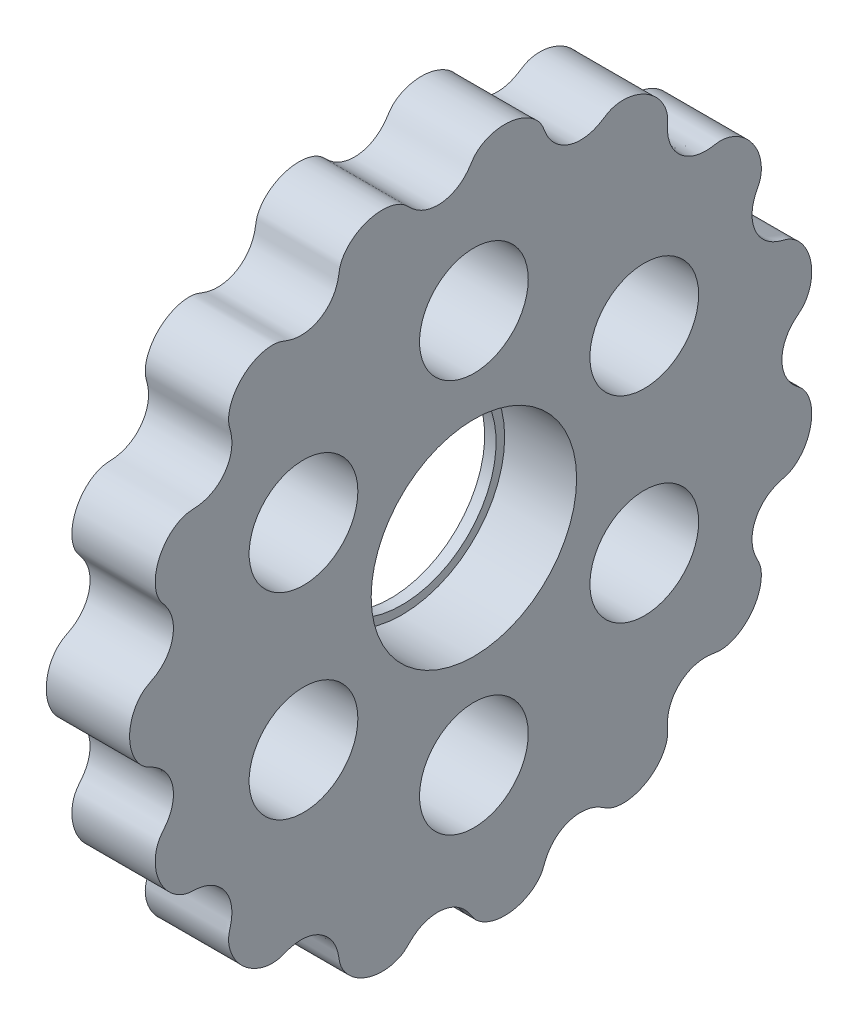
SolidWorks part; units mm, degrees
ref_plane "Front Plane" through (0, 0, 0) normal (0, 0, 1) x (1, 0, 0)
ref_plane "Top Plane" through (0, 0, 0) normal (0, 1, 0) x (1, 0, 0)
ref_plane "Right Plane" through (0, 0, 0) normal (1, 0, 0) x (0, 0, -1)
sketch "Sketch2" plane through (0, 0, 0) normal (0, 0, 1) x (1, 0, 0)
  line L0 (0, 0) -> (58.591, 0) construction
  line L2 (0, 0) -> (18.4, 0)
  line L3 (0, 0) -> (0, 2.5)
  line L4 (0, 2.5) -> (18.4, 2.5)
  line L5 (18.4, 0) -> (18.4, 2.5)
  line L6 (6.0094, 2.5) -> (6.0094, 6)
  line L11 (6.0094, 6) -> (9.9794, 6)
  line L16 (12.9794, 6) -> (12.9794, 3)
  line L17 (12.9794, 3) -> (13.6398, 3)
  line L18 (13.6398, 3) -> (13.6398, 2.5)
  line L19 (13.6398, 2.5) -> (6.0094, 2.5)
  line L22 (13.6398, 2.5) -> (16.1198, 2.5)
  line L23 (13.6398, 2.5) -> (13.6398, 4)
  line L24 (13.6398, 4) -> (16.1198, 4)
  line L25 (16.1198, 2.5) -> (16.1198, 4)
  line L27 (6.0094, 6) -> (9.9794, 6)
  line L28 (6.0094, 6) -> (6.0094, 9)
  line L29 (6.0094, 9) -> (9.9794, 9)
  line L30 (9.9794, 6) -> (9.9794, 9)
  line L31 (6.0094, 9) -> (6.0094, 8.25)
  line L32 (6.0094, 8.25) -> (5.0094, 8.25)
  line L33 (8.6609, 22.001) -> (8.6609, 12.476) construction
  line L34 (5.0094, 12.476) -> (12.3124, 12.476)
  line L35 (9.9794, 9) -> (12.3124, 9)
  line L36 (5.0094, 7.9375) -> (1.7709, 7.9375)
  line L37 (5.0094, 8.25) -> (5.0094, 12.476)
  line L38 (5.0094, 7.9375) -> (5.0094, 13.9365)
  line L39 (5.0094, 13.9365) -> (1.7709, 13.9365)
  line L40 (1.7709, 7.9375) -> (1.7709, 13.9365)
  line L41 (5.0094, 22.001) -> (12.3124, 22.001)
  line L42 (5.0094, 22.001) -> (5.0094, 30.1625)
  line L43 (5.0094, 30.1625) -> (12.3124, 30.1625)
  line L44 (12.3124, 22.001) -> (12.3124, 30.1625)
  line L49 (16.6398, 22.001) -> (16.6398, 7.5)
  line L51 (23.0198, 7.5) -> (23.0198, 6.5)
  line L54 (16.1198, 4) -> (13.6398, 4)
  line L56 (18.0398, 7.5) -> (23.0198, 7.5)
  line L57 (13.3124, 22.001) -> (16.6398, 22.001)
  line L58 (16.1198, 3.5) -> (20.0198, 3.5)
  line L59 (29.9098, 14) -> (26.9098, 11)
  line L60 (4.0094, 31.75) -> (18.0398, 31.75)
  line L61 (18.0398, 7.5) -> (23.0198, 7.5)
  line L62 (18.0398, 7.5) -> (18.0398, 12)
  line L63 (18.0398, 12) -> (23.0198, 12)
  line L64 (23.0198, 7.5) -> (23.0198, 12)
  line L65 (18.0398, 31.75) -> (18.0398, 12)
  line L66 (23.0198, 11) -> (26.9098, 11)
  line L67 (34.8098, 23) -> (31.3098, 19.5)
  line L68 (35.8098, 31) -> (38.7998, 33.99)
  line L69 (29.9098, 14) -> (29.9098, 15)
  line L70 (29.9098, 15) -> (22.9398, 15)
  line L71 (22.9398, 15) -> (21.0398, 15)
  line L72 (18.0398, 7.5) -> (16.6398, 7.5)
  line L73 (21.0398, 15) -> (21.0398, 43)
  line L74 (19.6115, 40) -> (9.6516, 40)
  line L75 (9.6516, 40) -> (4.0094, 40)
  line L76 (21.0398, 43) -> (19.6115, 43)
  line L77 (22.9398, 15) -> (29.9098, 15)
  line L78 (22.9398, 15) -> (22.9398, 21)
  line L79 (22.9398, 21) -> (29.9098, 21)
  line L80 (29.9098, 15) -> (29.9098, 21)
  line L81 (9.6516, 40) -> (19.6115, 40)
  line L82 (9.6516, 40) -> (9.6516, 50)
  line L83 (9.6516, 50) -> (19.6115, 50)
  line L84 (19.6115, 40) -> (19.6115, 50)
  line L85 (4.0094, 40) -> (4.0094, 31.75)
  line L86 (12.9794, 3) -> (12.9794, 2.5)
  line L87 (31.3098, 19.5) -> (29.9098, 19.5)
  line L88 (21.4694, 63.5) -> (21.4694, 51.308)
  line L89 (21.4694, 63.5) -> (25.9398, 63.5)
  line L90 (25.9398, 63.5) -> (25.9398, 25)
  line L91 (27.8398, 25) -> (25.9398, 25)
  line L92 (9.6516, 48) -> (8.2233, 48)
  line L93 (8.2233, 48) -> (8.2233, 53.476)
  line L94 (8.2233, 53.476) -> (19.6115, 53.476)
  line L95 (19.6115, 53.476) -> (19.6115, 50)
  line L96 (13.9174, 63.001) -> (13.9174, 53.476) construction
  line L97 (8.2233, 63.001) -> (19.6115, 63.001)
  line L98 (8.2233, 63.001) -> (8.2233, 68.2625)
  line L99 (8.2233, 68.2625) -> (19.6115, 68.2625)
  line L100 (19.6115, 63.001) -> (19.6115, 68.2625)
  line L101 (12.9794, 6) -> (11.9794, 6)
  line L102 (8.2233, 44.825) -> (4.9848, 44.825)
  line L103 (8.2233, 44.825) -> (8.2233, 54.9365)
  line L104 (8.2233, 54.9365) -> (4.9848, 54.9365)
  line L106 (9.9794, 6) -> (10.8794, 6)
  line L107 (27.8398, 25) -> (34.8098, 25)
  line L108 (34.8098, 25) -> (34.8098, 23)
  line L109 (0, 0) -> (-2, 0)
  line L110 (0, 0) -> (0, 11)
  line L111 (27.8398, 25) -> (34.8098, 25)
  line L112 (27.8398, 25) -> (27.8398, 32.5)
  line L113 (27.8398, 32.5) -> (34.8098, 32.5)
  line L114 (34.8098, 25) -> (34.8098, 32.5)
  line L115 (35.8098, 31) -> (34.8098, 31)
  line L116 (27.8398, 32.5) -> (27.8398, 64.5)
  line L117 (20.5849, 74.025) -> (6.2499, 74.025)
  line L118 (6.2499, 74.025) -> (6.2499, 76.2)
  line L119 (38.7998, 47.29) -> (30.8398, 55.25)
  line L120 (0, 11) -> (-2, 11)
  line L121 (38.7998, 43.815) -> (30.8623, 43.815)
  line L123 (-4.8152, 69.85) -> (1.5348, 76.2)
  line L124 (38.7998, 47.29) -> (38.7998, 33.99)
  line L125 (-2, 0) -> (-2, 11)
  line L126 (38.7998, 37.465) -> (30.8623, 37.465)
  line L127 (30.8623, 43.815) -> (30.8623, 37.465)
  line L128 (6.0094, 2.5) -> (6.0094, 0)
  line L129 (-0.0152, 63.5) -> (-0.0152, 30)
  line L132 (4.9848, 63.5) -> (-0.0152, 63.5)
  line L136 (-1.8152, 30) -> (-11.7752, 30)
  line L138 (-13.7752, 25.4) -> (-2, 25.4)
  line L139 (-2, 25.4) -> (-2, 11.5)
  line L140 (27.8398, 64.5) -> (20.5849, 64.5)
  line L141 (-1.8152, 30) -> (-11.7752, 30)
  line L142 (-1.8152, 30) -> (-1.8152, 39)
  line L143 (-1.8152, 39) -> (-11.7752, 39)
  line L144 (-11.7752, 30) -> (-11.7752, 39)
  line L145 (20.5849, 64.5) -> (20.5849, 74.025)
  line L146 (-12.7752, 37) -> (-12.7752, 47.29)
  line L147 (-12.7752, 37) -> (-11.7752, 37)
  line L148 (30.8398, 55.25) -> (30.8398, 76.2)
  line L149 (11.9794, 6) -> (11.9794, 5.45)
  line L154 (-2, 11.5) -> (0.5, 11.5)
  line L155 (4.9848, 60.6197) -> (24.0348, 60.6197)
  line L160 (4.9848, 60.6197) -> (4.9848, 55.8572)
  line L161 (4.9848, 55.8572) -> (24.0348, 55.8572)
  line L166 (24.0348, 60.6197) -> (24.0348, 55.8572)
  line L167 (4.9848, 60.6197) -> (24.0348, 55.8572) construction
  line L172 (4.9848, 55.8572) -> (24.0348, 60.6197) construction
  line L173 (24.0348, 62.2072) -> (25.9398, 62.2072)
  line L174 (11.9794, 5.45) -> (10.8794, 5.45)
  line L175 (10.8794, 6) -> (10.8794, 5.45)
  line L176 (24.0348, 62.2072) -> (24.0348, 54.2697)
  line L177 (24.0348, 54.2697) -> (25.9398, 54.2697)
  line L178 (25.9398, 62.2072) -> (25.9398, 54.2697)
  line L179 (24.0348, 62.2072) -> (25.9398, 54.2697) construction
  line L180 (24.0348, 54.2697) -> (25.9398, 62.2072) construction
  line L181 (3, 19.6197) -> (15.7, 19.6197)
  line L182 (3, 19.6197) -> (3, 14.8572)
  line L183 (3, 14.8572) -> (15.7, 14.8572)
  line L184 (15.7, 19.6197) -> (15.7, 14.8572)
  line L185 (3, 19.6197) -> (15.7, 14.8572) construction
  line L186 (3, 14.8572) -> (15.7, 19.6197) construction
  line L187 (15.7, 21.2072) -> (16.6398, 21.2072)
  line L188 (15.7, 21.2072) -> (15.7, 13.2697)
  line L189 (15.7, 13.2697) -> (16.6398, 13.2697)
  line L190 (16.6398, 21.2072) -> (16.6398, 13.2697)
  line L191 (15.7, 21.2072) -> (16.6398, 13.2697) construction
  line L192 (15.7, 13.2697) -> (16.6398, 21.2072) construction
  line L193 (0.5, 11.5) -> (0.5, 6.9375)
  line L194 (0.5, 6.9375) -> (1.7709, 6.9375)
  line L195 (23.0198, 6.5) -> (20.0198, 3.5)
  line L196 (4.9848, 63.5) -> (4.9848, 54.9365)
  line L197 (3, 43.825) -> (4.9848, 43.825)
  line L198 (1.7709, 6.9375) -> (1.7709, 7.9375)
  line L199 (6.0094, 0) -> (12.9794, 0)
  line L200 (12.9794, 0) -> (12.9794, 2.5)
  line L201 (18.0398, 31.75) -> (18.0398, 35.875)
  line L202 (18.0398, 35.875) -> (21.0398, 35.875)
  line L203 (30.8398, 76.2) -> (6.2499, 76.2)
  line L204 (2.8049, 69.85) -> (7.2499, 69.85) construction
  line L205 (7.2499, 67.4688) -> (26.2999, 67.4688)
  line L206 (7.2499, 74.025) -> (7.2499, 64.5)
  line L207 (7.2499, 64.5) -> (-1.8152, 64.5)
  line L208 (-1.8152, 64.5) -> (-1.8152, 39)
  line L209 (-12.7752, 47.29) -> (-4.8152, 55.25)
  line L210 (-4.8152, 55.25) -> (-4.8152, 69.85)
  line L211 (7.2499, 67.4688) -> (7.2499, 72.2312)
  line L212 (7.2499, 72.2312) -> (26.2999, 72.2313)
  line L213 (26.2999, 67.4688) -> (26.2999, 72.2313)
  line L214 (26.2999, 73.8187) -> (30.8398, 73.8187)
  line L215 (26.2999, 73.8187) -> (26.2999, 65.8813)
  line L216 (26.2999, 65.8813) -> (30.8398, 65.8813)
  line L217 (30.8398, 73.8187) -> (30.8398, 65.8813)
  line L218 (2.8049, 72.2313) -> (25.0299, 72.2313)
  line L219 (2.8049, 72.2313) -> (2.8049, 67.4687)
  line L220 (2.8049, 67.4687) -> (25.0299, 67.4687)
  line L221 (25.0299, 72.2313) -> (25.0299, 67.4687)
  line L222 (25.0299, 69.85) -> (20.5849, 69.85) construction
  line L223 (21.4694, 51.308) -> (22.9398, 51.308)
  line L224 (22.9398, 51.308) -> (22.9398, 21)
  line L225 (13.6398, 4) -> (13.6398, 12.2697)
  line L226 (13.6398, 12.2697) -> (13.3124, 12.2697)
  line L227 (13.3124, 12.2697) -> (13.3124, 22.001)
  line L228 (12.3124, 9) -> (12.3124, 12.476)
  line L229 (-1.8152, 30) -> (-0.0152, 30)
  line L230 (8.2233, 65.6317) -> (2.8049, 65.6317) construction
  line L231 (19.6115, 65.6317) -> (25.0299, 65.6317) construction
  line L232 (1.5348, 76.2) -> (6.2499, 76.2)
  line L233 (-11.7752, 30) -> (-13.7752, 30)
  line L234 (-13.7752, 30) -> (-13.7752, 25.4)
  line L235 (3, 13.9365) -> (3, 43.825)
  line L236 (4.9848, 54.9365) -> (4.9848, 44.825)
  line L237 (4.9848, 43.825) -> (4.9848, 44.825)
  circle A0 centre (26.8898, 25.95) radius 0.95
  circle A1 centre (21.9898, 15.95) radius 0.95
  circle A2 centre (17.3398, 8.2) radius 0.7
  circle A3 centre (10.4294, 6.45) radius 0.45
  circle A4 centre (-0.9152, 30.9) radius 0.9
  point P7 (24.9873, 58.2385)
  point P131 (16.1699, 17.2385)
  point P135 (14.5098, 58.2385)
  point P146 (9.35, 17.2385)
sketch "Sketch3" plane through (0, 0, 0) normal (1, 0, 0) x (0, 0, -1)
  line L0 (0, 0) -> (0, 69.85) construction
  line L1 (0, 0) -> (13.6271, 68.5079) construction
  line L2 (0, 0) -> (0, 58.2385) construction
  line L3 (0, 0) -> (50.436, 29.1192) construction
  line L4 (0, 0) -> (0, 31.75) construction
  line L5 (0, 0) -> (12.1502, 29.3332) construction
  line L6 (0, 0) -> (0, 17.2385) construction
  line L7 (0, 0) -> (14.929, 8.6192) construction
  line L8 (0, 0) -> (0, 58.2385) construction
  line L9 (0, 0) -> (50.436, 29.1192) construction
  line L10 (0, 0) -> (5.9583, 29.9542) construction
  line L11 (0, 0) -> (16.9677, 25.394) construction
  circle A0 centre (0, 0) radius 69.85 construction
  circle A1 centre (0, 0) radius 58.2385 construction
  circle A2 centre (0, 0) radius 31.75 construction
  circle A3 centre (0, 0) radius 17.2385 construction
  circle A4 centre (0, 69.85) radius 3.175
  circle A5 centre (0, 58.2385) radius 4.7625
  circle A6 centre (0, 31.75) radius 3.175
  circle A7 centre (0, 17.2385) radius 4.7625
  circle A8 centre (13.6271, 68.5079) radius 3.175
  circle A9 centre (26.7304, 64.533) radius 3.175
  circle A10 centre (38.8066, 58.0782) radius 3.175
  circle A11 centre (49.3914, 49.3914) radius 3.175
  circle A12 centre (58.0782, 38.8066) radius 3.175
  circle A13 centre (64.533, 26.7304) radius 3.175
  circle A14 centre (68.5079, 13.6271) radius 3.175
  circle A15 centre (69.85, 0) radius 3.175
  circle A16 centre (68.5079, -13.6271) radius 3.175
  circle A17 centre (64.533, -26.7304) radius 3.175
  circle A18 centre (58.0782, -38.8066) radius 3.175
  circle A19 centre (49.3914, -49.3914) radius 3.175
  circle A20 centre (38.8066, -58.0782) radius 3.175
  circle A21 centre (26.7304, -64.533) radius 3.175
  circle A22 centre (13.6271, -68.5079) radius 3.175
  circle A23 centre (0, -69.85) radius 3.175
  circle A24 centre (-13.6271, -68.5079) radius 3.175
  circle A25 centre (-26.7304, -64.533) radius 3.175
  circle A26 centre (-38.8066, -58.0782) radius 3.175
  circle A27 centre (-49.3914, -49.3914) radius 3.175
  circle A28 centre (-58.0782, -38.8066) radius 3.175
  circle A29 centre (-64.533, -26.7304) radius 3.175
  circle A30 centre (-68.5079, -13.6271) radius 3.175
  circle A31 centre (-69.85, 0) radius 3.175
  circle A32 centre (-68.5079, 13.6271) radius 3.175
  circle A33 centre (-64.533, 26.7304) radius 3.175
  circle A34 centre (-58.0782, 38.8066) radius 3.175
  circle A35 centre (-49.3914, 49.3914) radius 3.175
  circle A36 centre (-38.8066, 58.0782) radius 3.175
  circle A37 centre (-26.7304, 64.533) radius 3.175
  circle A38 centre (-13.6271, 68.5079) radius 3.175
  circle A47 centre (50.436, 29.1192) radius 4.7625
  circle A48 centre (50.436, -29.1192) radius 4.7625
  circle A49 centre (0, -58.2385) radius 4.7625
  circle A50 centre (-50.436, -29.1192) radius 4.7625
  circle A51 centre (-50.436, 29.1192) radius 4.7625
  circle A58 centre (12.1502, 29.3332) radius 3.175
  circle A59 centre (22.4506, 22.4506) radius 3.175
  circle A60 centre (29.3332, 12.1502) radius 3.175
  circle A61 centre (31.75, 0) radius 3.175
  circle A62 centre (29.3332, -12.1502) radius 3.175
  circle A63 centre (22.4506, -22.4506) radius 3.175
  circle A64 centre (12.1502, -29.3332) radius 3.175
  circle A65 centre (0, -31.75) radius 3.175
  circle A66 centre (-12.1502, -29.3332) radius 3.175
  circle A67 centre (-22.4506, -22.4506) radius 3.175
  circle A68 centre (-29.3332, -12.1502) radius 3.175
  circle A69 centre (-31.75, 0) radius 3.175
  circle A70 centre (-29.3332, 12.1502) radius 3.175
  circle A71 centre (-22.4506, 22.4506) radius 3.175
  circle A72 centre (14.929, 8.6192) radius 4.7625
  circle A73 centre (14.929, -8.6192) radius 4.7625
  circle A74 centre (0, -17.2385) radius 4.7625
  circle A75 centre (-14.929, -8.6192) radius 4.7625
  circle A76 centre (-14.929, 8.6192) radius 4.7625
  circle A77 centre (0, 0) radius 50
  circle A78 centre (0, 0) radius 9
  circle A79 centre (-12.1502, 29.3332) radius 3.175
  circle A80 centre (0, 0) radius 76.2
  circle A81 centre (0, 0) radius 74.025
  circle A82 centre (0, 69.85) radius 3.9687
  circle A83 centre (49.3914, 49.3914) radius 3.9687
  circle A84 centre (69.85, 0) radius 3.9688
  circle A85 centre (49.3914, -49.3914) radius 3.9687
  circle A86 centre (0, -69.85) radius 3.9687
  circle A87 centre (-49.3914, -49.3914) radius 3.9687
  circle A88 centre (-69.85, 0) radius 3.9688
  circle A89 centre (-49.3914, 49.3914) radius 3.9687
  circle A90 centre (0, 69.85) radius 2.3812
  circle A91 centre (13.6271, 68.5079) radius 2.3812
  circle A92 centre (26.7304, 64.533) radius 2.3813
  circle A93 centre (38.8066, 58.0782) radius 2.3812
  circle A94 centre (49.3914, 49.3914) radius 2.3812
  circle A95 centre (58.0782, 38.8066) radius 2.3812
  circle A96 centre (64.533, 26.7304) radius 2.3813
  circle A97 centre (68.5079, 13.6271) radius 2.3813
  circle A98 centre (69.85, 0) radius 2.3813
  circle A99 centre (68.5079, -13.6271) radius 2.3813
  circle A100 centre (64.533, -26.7304) radius 2.3813
  circle A101 centre (58.0782, -38.8066) radius 2.3812
  circle A102 centre (49.3914, -49.3914) radius 2.3812
  circle A103 centre (38.8066, -58.0782) radius 2.3812
  circle A104 centre (26.7304, -64.533) radius 2.3813
  circle A105 centre (13.6271, -68.5079) radius 2.3812
  circle A106 centre (0, -69.85) radius 2.3812
  circle A107 centre (-13.6271, -68.5079) radius 2.3812
  circle A108 centre (-26.7304, -64.533) radius 2.3813
  circle A109 centre (-38.8066, -58.0782) radius 2.3812
  circle A110 centre (-49.3914, -49.3914) radius 2.3812
  circle A111 centre (-58.0782, -38.8066) radius 2.3812
  circle A112 centre (-64.533, -26.7304) radius 2.3812
  arc A113 (3.0399, 30.8338) -> (8.9911, 29.65) centre (5.9583, 29.9542) cw
  arc A114 (14.6081, 27.3234) -> (19.6532, 23.9523) centre (16.9677, 25.394) cw
  arc A115 (23.9523, 19.6532) -> (27.3234, 14.6081) centre (25.394, 16.9677) cw
  arc A116 (29.65, 8.9911) -> (30.8338, 3.0399) centre (29.9542, 5.9583) cw
  arc A117 (30.8338, -3.0399) -> (29.65, -8.9911) centre (29.9542, -5.9583) cw
  arc A118 (27.3234, -14.6081) -> (23.9523, -19.6532) centre (25.394, -16.9677) cw
  arc A119 (19.6532, -23.9523) -> (14.6081, -27.3234) centre (16.9677, -25.394) cw
  arc A120 (8.9911, -29.65) -> (3.0399, -30.8338) centre (5.9583, -29.9542) cw
  arc A121 (-3.0399, -30.8338) -> (-8.9911, -29.65) centre (-5.9583, -29.9542) cw
  arc A122 (-14.6081, -27.3234) -> (-19.6532, -23.9523) centre (-16.9677, -25.394) cw
  arc A123 (-23.9523, -19.6532) -> (-27.3234, -14.6081) centre (-25.394, -16.9677) cw
  arc A124 (-29.65, -8.9911) -> (-30.8338, -3.0399) centre (-29.9542, -5.9583) cw
  arc A125 (-30.8338, 3.0399) -> (-29.65, 8.9911) centre (-29.9542, 5.9583) cw
  arc A126 (-27.3234, 14.6081) -> (-23.9523, 19.6532) centre (-25.394, 16.9677) cw
  arc A127 (-19.6532, 23.9523) -> (-14.6081, 27.3234) centre (-16.9677, 25.394) cw
  arc A128 (-8.9911, 29.65) -> (-3.0399, 30.8338) centre (-5.9583, 29.9542) cw
  arc A129 (26.9875, 0) -> (26.9932, 0.1932) centre (30.2705, 0) cw
  arc A130 (65.0988, 0.2771) -> (65.0875, 0) centre (68.4964, 0) ccw
  circle A131 centre (1.5875, 0) radius 40
  circle A132 centre (1.5875, 0) radius 2.5
  circle A133 centre (1.5875, 0) radius 3
  circle A134 centre (1.5875, 0) radius 43
  circle A135 centre (-68.5079, -13.6271) radius 2.3813
  circle A136 centre (-69.85, 0) radius 2.3813
  circle A137 centre (-68.5079, 13.6271) radius 2.3813
  circle A138 centre (-64.533, 26.7304) radius 2.3812
  circle A139 centre (-58.0782, 38.8066) radius 2.3812
  circle A140 centre (-49.3914, 49.3914) radius 2.3812
  circle A141 centre (-38.8066, 58.0782) radius 2.3812
  circle A142 centre (-26.7304, 64.533) radius 2.3813
  circle A143 centre (-13.6271, 68.5079) radius 2.3812
  circle A144 centre (0, 58.2385) radius 2.3812
  circle A145 centre (0, 58.2385) radius 3.9688
  circle A146 centre (50.436, 29.1192) radius 3.9688
  circle A147 centre (50.436, 29.1192) radius 2.3813
  circle A148 centre (50.436, -29.1192) radius 3.9687
  circle A149 centre (50.436, -29.1192) radius 2.3812
  circle A150 centre (0, -58.2385) radius 3.9687
  circle A151 centre (0, -58.2385) radius 2.3812
  circle A152 centre (-50.436, -29.1192) radius 3.9687
  circle A153 centre (-50.436, -29.1192) radius 2.3812
  circle A154 centre (-50.436, 29.1192) radius 3.9687
  circle A155 centre (-50.436, 29.1192) radius 2.3812
  spline S1 degree 4 number of poles 499 (26.9875, 0) -> (26.9932, 0.1932)
  spline S3 degree 4 number of poles 617 (65.0875, 0) -> (65.0988, 0.2771)
  point P116 (0, 0)
  point P225 (0, 0)
sketch "Sketch4" plane through (0, 0, 0) normal (0, 0, 1) x (1, 0, 0)
  line L0 (6.0094, 9) -> (9.9794, 9) construction
  line L1 (9.9794, 9) -> (12.3124, 9) construction
  line L2 (12.3124, 9) -> (12.3124, 12.476) construction
  line L3 (6.0094, 9) -> (9.9794, 9)
  line L4 (6.0094, 6) -> (6.0094, 9) construction
  line L7 (5.0094, 12.476) -> (12.3124, 12.476) construction
  line L8 (5.0094, 8.25) -> (5.0094, 12.476) construction
  line L9 (6.0094, 8.25) -> (5.0094, 8.25) construction
  line L14 (6.0094, 8.25) -> (6.0094, 9)
  line L17 (5.0094, 12.476) -> (12.3124, 12.476)
  line L18 (5.0094, 8.25) -> (5.0094, 12.476)
  line L19 (6.0094, 8.25) -> (5.0094, 8.25)
  line L20 (9.9794, 9) -> (12.3124, 9)
  line L21 (12.3124, 9) -> (12.3124, 12.476)
revolve "Revolve1" add sketch "Sketch4" angle 360 about L0
sketch "Sketch6" plane through (0, 0, 0) normal (1, 0, 0) x (0, 0, -1)
  circle A0 centre (-14.929, -8.6192) radius 4.7625 construction
  circle A1 centre (0, -17.2385) radius 4.7625 construction
  circle A2 centre (14.929, -8.6192) radius 4.7625 construction
  circle A3 centre (14.929, 8.6192) radius 4.7625 construction
  circle A4 centre (0, 17.2385) radius 4.7625 construction
  circle A5 centre (-14.929, 8.6192) radius 4.7625 construction
  circle A6 centre (-14.929, -8.6192) radius 4.7625
  circle A7 centre (0, -17.2385) radius 4.7625
  circle A8 centre (14.929, -8.6192) radius 4.7625
  circle A9 centre (14.929, 8.6192) radius 4.7625
  circle A10 centre (0, 17.2385) radius 4.7625
  circle A11 centre (-14.929, 8.6192) radius 4.7625
  circle A12 centre (0, 0) radius 9 construction
  circle A13 centre (0, 0) radius 9
  arc A14 (26.9932, 0.1932) -> (26.9875, 0) centre (30.2705, 0) ccw construction
  arc A15 (26.9932, 0.1932) -> (26.9875, 0) centre (30.2705, 0) ccw
  spline S0 degree 4 number of poles 499 (26.9875, 0) -> (26.9932, 0.1932) construction
  spline S1 degree 4 number of poles 499 (26.9875, 0) -> (26.9932, 0.1932)
extrude "Boss-Extrude1" add sketch "Sketch6" along normal up to vertex (5 mm away) from vertex contours S1 A15 A13 A11 A10 A9 A8 A7 A6
